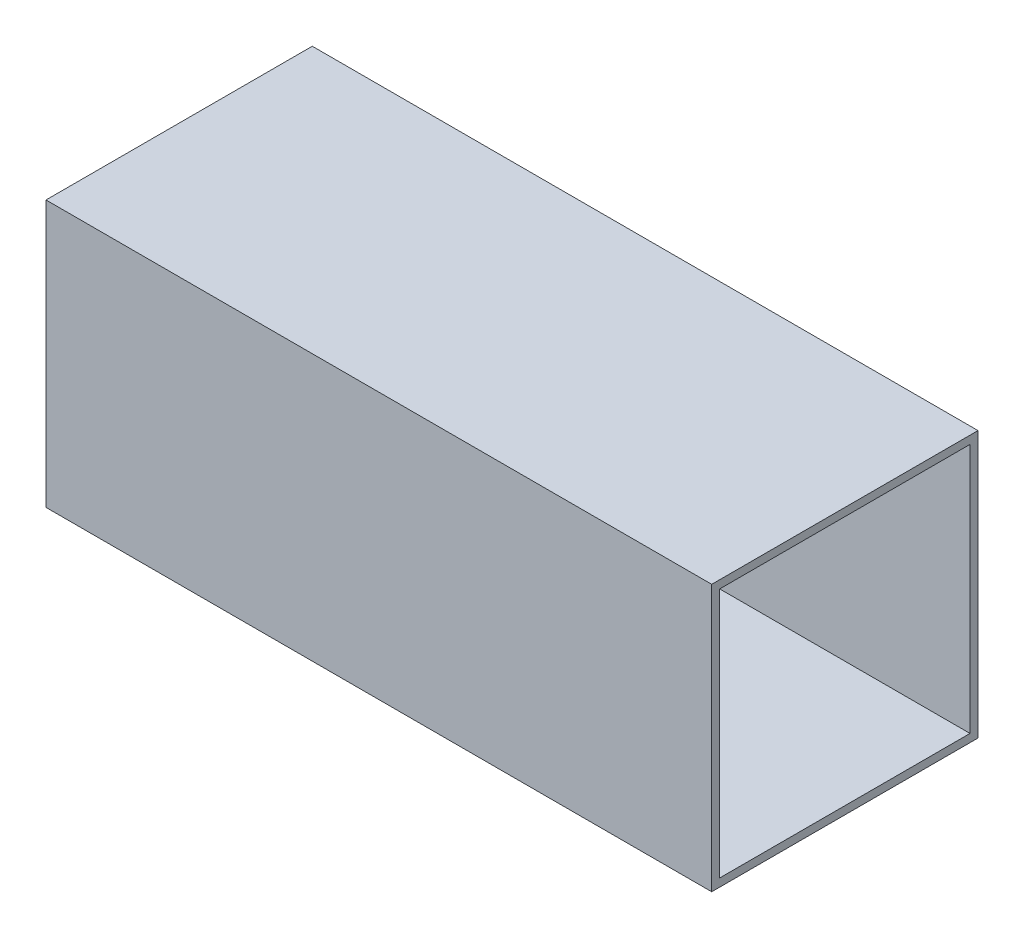
SolidWorks part; units mm, degrees
ref_plane "Alzado" through (0, 0, 0) normal (0, 0, 1) x (1, 0, 0)
ref_plane "Planta" through (0, 0, 0) normal (0, 1, 0) x (1, 0, 0)
ref_plane "Vista lateral" through (0, 0, 0) normal (1, 0, 0) x (0, 0, -1)
sketch "Croquis1" plane through (0, 0, 0) normal (0, 0, 1) x (1, 0, 0)
  line L1 (0, 100) -> (250, 100)
  line L2 (0, 100) -> (0, 0)
  line L3 (0, 0) -> (250, 0)
  line L4 (250, 100) -> (250, 0)
  dimension "D1" = 100
  dimension "D2" = 250
extrude "Saliente-Extruir1" add sketch "Croquis1" along normal blind 100
shell "Vaciado1" thickness 3
sketch "Croquis2" plane through (0, 0, 3) normal (0, 0, 1) x (1, 0, 0)
  line L0 (35, 38.9909) -> (111.1669, 65.3499)
  line L1 (169, 35) -> (49, 35)
  line L2 (49, 35) -> (35, 38.9909)
  line L3 (0, 97) -> (0, 3) construction
  arc A0 (111.1669, 65.3499) -> (175.6501, 52.4683) centre (132.4244, 3.9241) cw
  arc A1 (175.6501, 52.4683) -> (169, 35) centre (169, 45) cw
  dimension "D3" = 10
  dimension "D4" = 65
  dimension "D1" = 120
  dimension "D2" = 35
  dimension "D5" = 14
  dimension "D6" = 30.3499
  dimension "D7" = 35
  dimension "D8" = 35
extrude "Saliente-Extruir2" add sketch "Croquis2" along normal up to next
